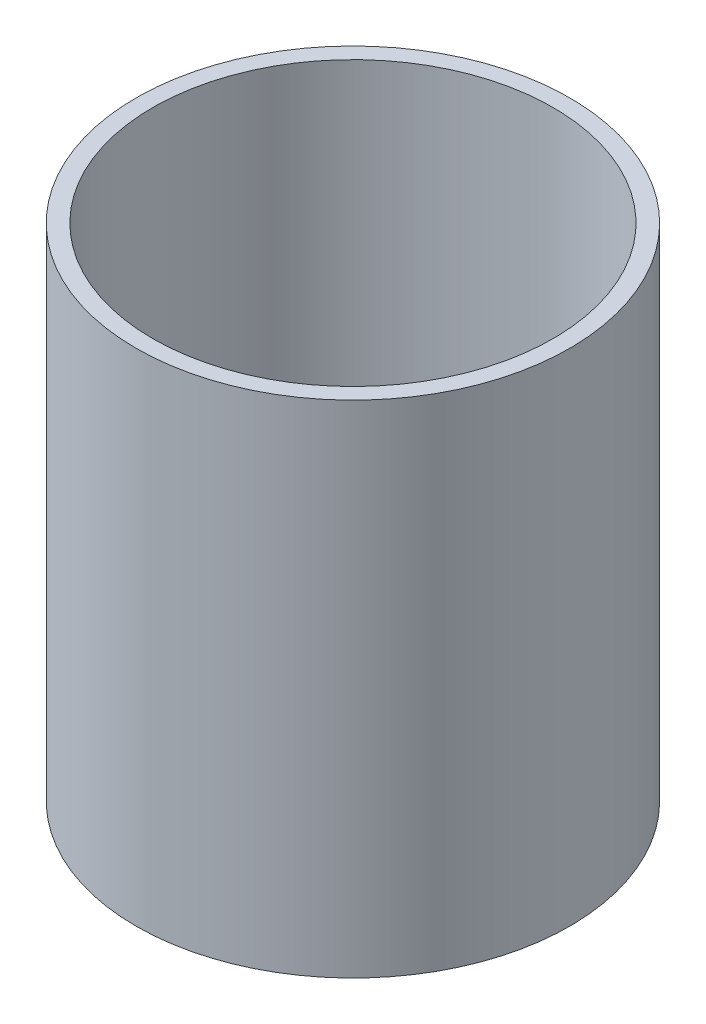
SolidWorks part; units mm, degrees
ref_plane "前视基准面" through (0, 0, 0) normal (0, 0, 1) x (1, 0, 0)
ref_plane "上视基准面" through (0, 0, 0) normal (0, 1, 0) x (1, 0, 0)
ref_plane "右视基准面" through (0, 0, 0) normal (1, 0, 0) x (0, 0, -1)
sketch "草图1" plane through (0, 0, 0) normal (0, 1, 0) x (1, 0, 0)
  circle A0 centre (0, 0) radius 24
  circle A1 centre (0, 0) radius 26
  dimension "D1" = 48
  dimension "D2" = 2
extrude "凸台-拉伸1" add sketch "草图1" along normal blind 70
sketch "Sketch1" plane through (0, 70, 0) normal (0, 1, 0) x (1, 0, 0)
  circle A0 centre (0, 0) radius 26
extrude "Cut-Extrude1" cut sketch "Sketch1" against normal blind 10
